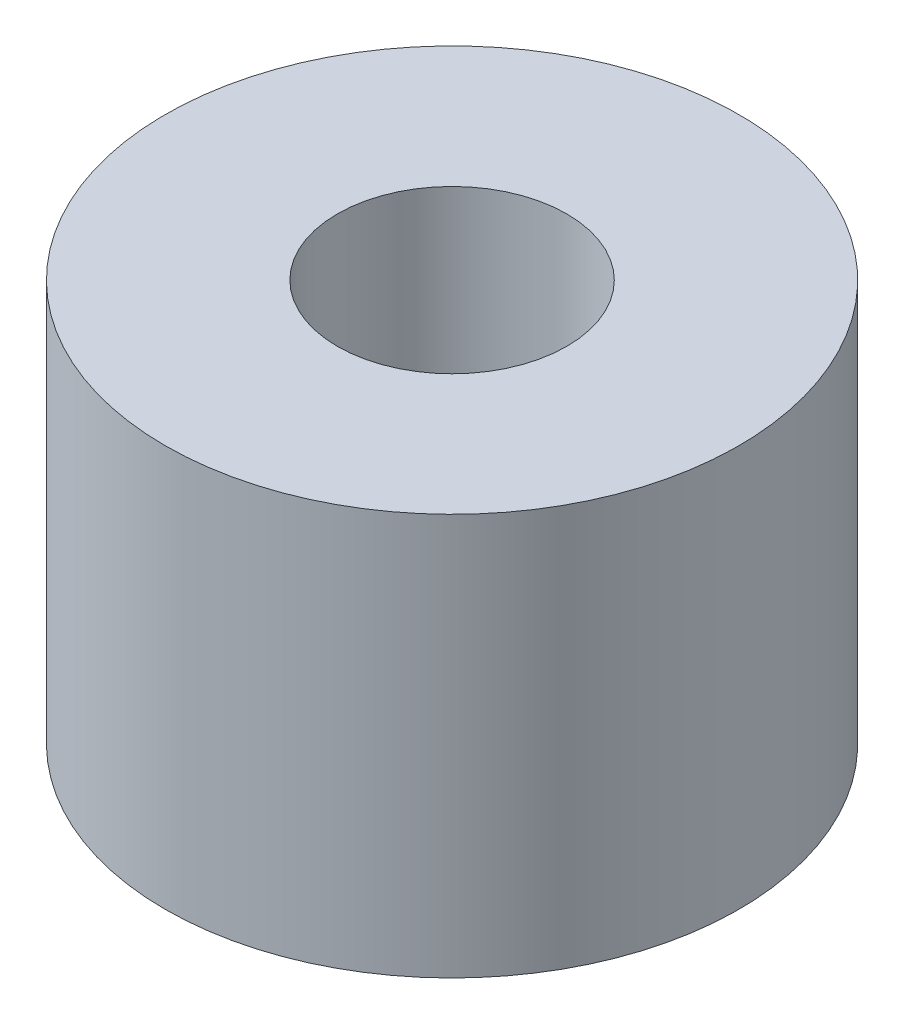
SolidWorks part; units mm, degrees
ref_plane "Plan de face" through (0, 0, 0) normal (0, 0, 1) x (1, 0, 0)
ref_plane "Plan de dessus" through (0, 0, 0) normal (0, 1, 0) x (1, 0, 0)
ref_plane "Plan de droite" through (0, 0, 0) normal (1, 0, 0) x (0, 0, -1)
sketch "Esquisse2" plane through (0, 0, 0) normal (0, 1, 0) x (1, 0, 0)
  circle A0 centre (0, 0) radius 25
  dimension "D1" = 50
extrude "Boss.-Extru.1" add sketch "Esquisse2" along normal blind 35
sketch "Esquisse3" plane through (0, 35, 0) normal (0, 1, 0) x (1, 0, 0)
  circle A0 centre (0, 0) radius 10
extrude "Enlèv. mat.-Extru.1" cut sketch "Esquisse3" against normal blind 35
hole_wizard "Trou taraudé M62" positions "Esquisse5" profile "Esquisse4" tap size "M6" standard "ISO"
sketch "Esquisse5" plane through (0, 0, 0) normal (0, -1, 0) x (-1, 0, 0)
  circle A0 centre (0, 0) radius 17.5
  point P5 (17.5, 0)
  point P7 (-8.7485, -15.1563)
  point P9 (-8.7531, 15.1537)
  point P22 (-8.8566, 15.0934)
  dimension "D1" = 35
  dimension "D2" = 30.31
  dimension "D3" = 30.31
sketch "Esquisse4" plane through (-17.5, 0, 0) normal (1, 0, 0) x (0, 0, -1)
  line L0 (0, 0) -> (0, 21.5022)
  line L1 (0, 21.5022) -> (2.5, 20)
  line L2 (2.5, 20) -> (2.5, 0)
  line L5 (2.5, 0) -> (0, 0)
  line L10 (0, 21.5022) -> (-2.5, 20) construction
  line L11 (0, -6.35) -> (0, 107.95) construction
  dimension "Diamètre du trou pour taraudage" = 5
  dimension "Profondeur du trou pour taraudage" = 20
  dimension "Angle de pointe" = 118
cosmetic thread "Filetage de perçage1" parameters "D1"=15, "D2"=6
cosmetic thread "Filetage de perçage2" parameters "D1"=15, "D2"=6
cosmetic thread "Filetage de perçage3" parameters "D1"=15, "D2"=6
